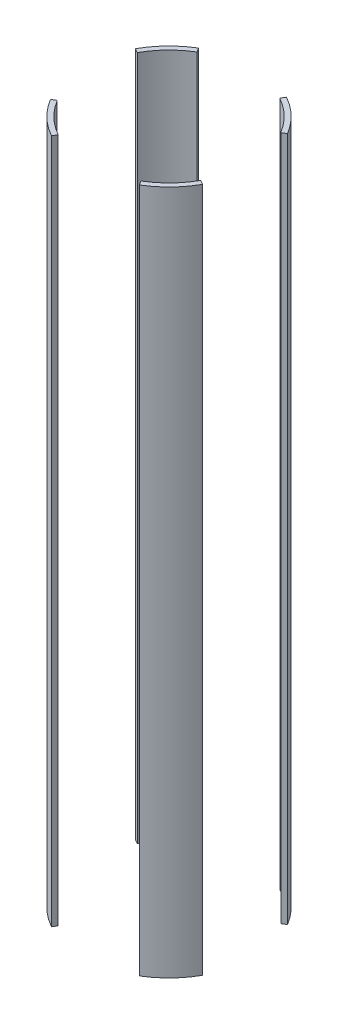
SolidWorks part; units mm, degrees
material "6061-T6 (SS)"
ref_plane "Front Plane" through (0, 0, 0) normal (0, 0, 1) x (1, 0, 0)
ref_plane "Top Plane" through (0, 0, 0) normal (0, 1, 0) x (1, 0, 0)
ref_plane "Right Plane" through (0, 0, 0) normal (1, 0, 0) x (0, 0, -1)
sketch "Sketch2" plane through (0, 0, 0) normal (0, 1, 0) x (1, 0, 0)
  circle A0 centre (0, 0) radius 88.9
  circle A1 centre (0, 0) radius 83.82
  dimension "D1" = 177.8
  dimension "D2" = 167.64
extrude "Boss-Extrude1" add sketch "Sketch2" along normal mid plane 704.85
sketch "Sketch3" plane through (0, 0, 0) normal (0, 1, 0) x (1, 0, 0)
  line L0 (0, 0) -> (169.6618, 101.6776)
  line L1 (-58.1167, 96.9749) -> (0, 0)
  line L2 (0, 0) -> (53.9, 96.9749)
  line L3 (53.9, 96.9749) -> (-58.1167, 96.9749)
  line L4 (0, 0) -> (70.9917, -118.4586)
  line L5 (70.9917, -118.4586) -> (-65.8409, -118.4586)
  line L6 (-65.8409, -118.4586) -> (0, 0)
  line L7 (169.6618, 101.6776) -> (169.6618, -94.3004)
  line L8 (169.6618, -94.3004) -> (0, 0)
  line L9 (0, 0) -> (-123.7413, 68.7771)
  line L10 (-123.7413, 68.7771) -> (-123.7413, -74.1577)
  line L11 (-123.7413, -74.1577) -> (0, 0)
  dimension "D1" = 60
  dimension "D2" = 60
  dimension "D3" = 60
  dimension "D4" = 60
  dimension "D5" = 30
  dimension "D6" = 30
extrude "Cut-Extrude1" cut sketch "Sketch3" against normal through all both and the other way through all contours L8 L7 L0 | L2 L3 L1 | L10 L11 L9 | L6 L5 L4
equation "\"D1@Boss-Extrude1\"=3*12"
